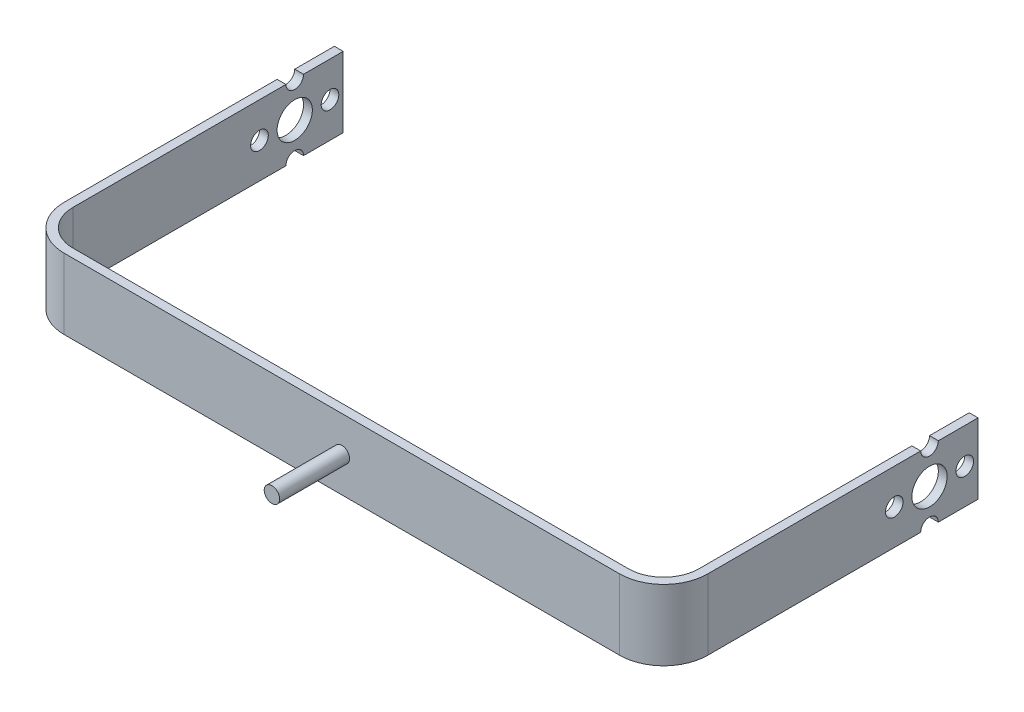
SolidWorks part; units mm, degrees
material "6061-T6 (SS)"
ref_plane "Front Plane" through (0, 0, 0) normal (0, 0, 1) x (1, 0, 0)
ref_plane "Top Plane" through (0, 0, 0) normal (0, 1, 0) x (1, 0, 0)
ref_plane "Right Plane" through (0, 0, 0) normal (1, 0, 0) x (0, 0, -1)
sketch "Sketch1" plane through (0, 0, 0) normal (0, 1, 0) x (1, 0, 0)
  line L0 (0, 0) -> (142.05, 0)
  line L1 (142.05, 0) -> (142.05, 69.325)
  line L2 (142.05, 69.325) -> (144.05, 69.325)
  line L3 (144.05, 69.325) -> (144.05, -2)
  line L4 (144.05, -2) -> (-2, -2)
  line L5 (-2, -2) -> (-2, 69.325)
  line L6 (-2, 69.325) -> (0, 69.325)
  line L7 (0, 69.325) -> (0, 0)
  line L8 (0, 0) -> (0, -2) construction
  dimension "D1" = 2
  dimension "D2" = 146.05
  dimension "D3" = 71.325
extrude "Boss-Extrude1" add sketch "Sketch1" along normal blind 16
fillet "Fillet1" radius 8 2 edges at (142.05, 8, 0) (0, 8, 0)
fillet "Fillet2" radius 10 2 edges at (-2, 8, 2) (144.05, 8, 2)
sketch "Sketch2" plane through (144.05, 0, 0) normal (1, 0, 0) x (0, 0, -1)
  line L0 (69.325, 8) -> (58.325, 8) construction
  line L1 (69.325, 16) -> (69.325, 0) construction
  line L2 (-2, 0) -> (-2, 16) construction
  circle A0 centre (58.325, 8) radius 4
  circle A1 centre (66.325, 8) radius 2
  circle A2 centre (58.325, 0) radius 2
  circle A3 centre (50.325, 8) radius 2
  circle A4 centre (58.325, 16) radius 2
  point P18 (58.325, 8)
  dimension "D1" = 8
  dimension "D3" = 4
  dimension "D2" = 60.325
  dimension "D4" = 8
  dimension "D5" = 4
extrude "Cut-Extrude1" cut sketch "Sketch2" against normal through all
sketch "Sketch3" plane through (0, 0, 2) normal (0, 0, 1) x (1, 0, 0)
  line L0 (8, 8) -> (134.05, 8) construction
  line L1 (8, 16) -> (8, 0) construction
  line L2 (134.05, 0) -> (134.05, 16) construction
  circle A0 centre (71.025, 8) radius 1.75
  dimension "D1" = 3.5
extrude "Boss-Extrude2" add sketch "Sketch3" along normal blind 15.875 contours A0
